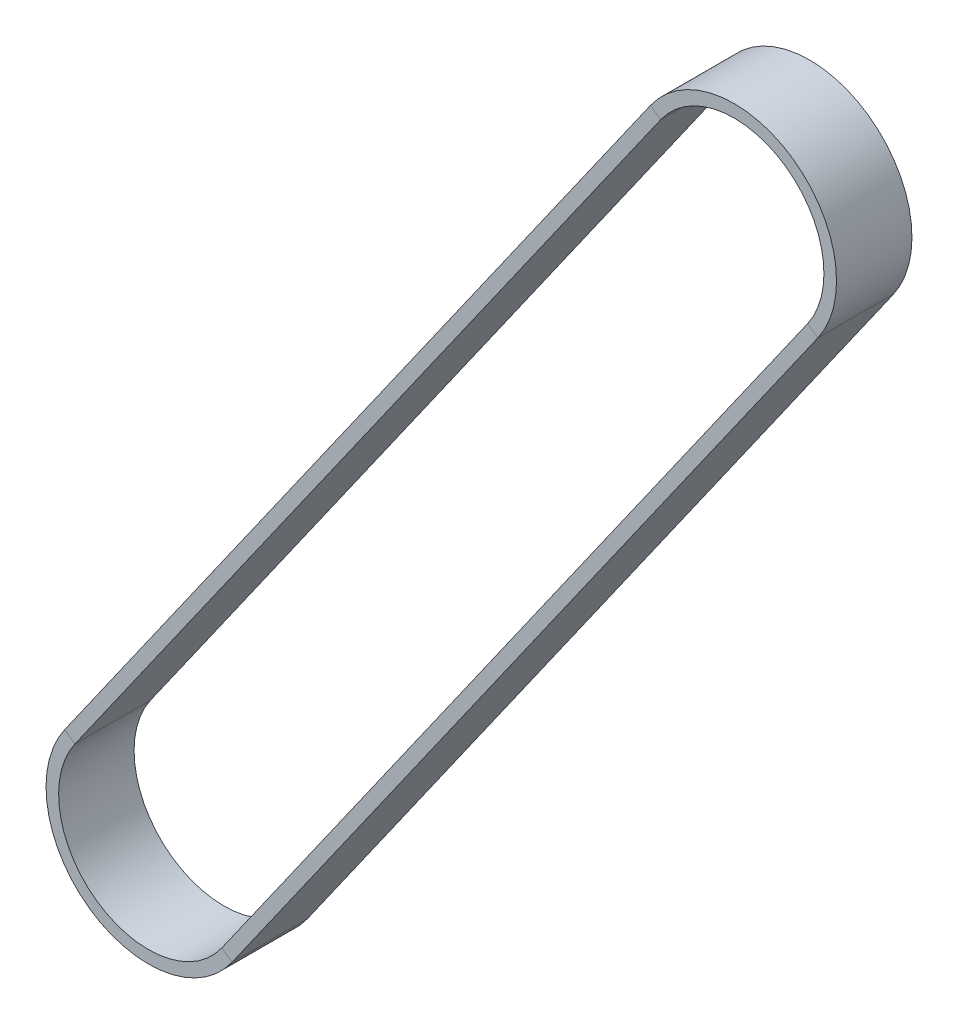
SolidWorks part; units mm, degrees
ref_plane "Front Plane" through (0, 0, 0) normal (0, 0, 1) x (1, 0, 0)
ref_plane "Top Plane" through (0, 0, 0) normal (0, 1, 0) x (1, 0, 0)
ref_plane "Right Plane" through (0, 0, 0) normal (1, 0, 0) x (0, 0, -1)
sketch "Sketch1" plane through (0, 0, 0) normal (0, 0, 1) x (1, 0, 0)
  line L0 (0, 0) -> (1, 0) construction
  line L1 (0, 0) -> (0, 1) construction
  line L2 (6.3191, 1.7623) -> (-63.5563, -97.6602)
  line L3 (-82.3008, -84.4863) -> (-12.4254, 14.9362)
  arc A0 (-12.4254, 14.9362) -> (6.3191, 1.7623) centre (-3.0532, 8.3493) cw
  arc A1 (-63.5563, -97.6602) -> (-82.3008, -84.4863) centre (-72.9286, -91.0733) cw
ref_plane "Plane1" through (-12.4254, 14.9362, 0) normal (0.575, 0.8181, 0) x (0.8181, -0.575, 0)
sketch "Sketch2" plane through (-12.4254, 14.9362, 0) normal (0.575, 0.8181, 0) x (0.8181, -0.575, 0)
  line L1 (0.75, -4.5) -> (-0.75, -4.5)
  line L2 (0.75, -4.5) -> (0.75, 4.5)
  line L3 (0.75, 4.5) -> (-0.75, 4.5)
  line L4 (-0.75, -4.5) -> (-0.75, 4.5)
  line L5 (0.75, -4.5) -> (-0.75, 4.5) construction
  line L6 (0.75, 4.5) -> (-0.75, -4.5) construction
  point P0 (0, 0)
  dimension "D1" = 9
  dimension "D2" = 1.5
sweep "Sweep1" add profiles "Sketch2" path "Sketch1"
